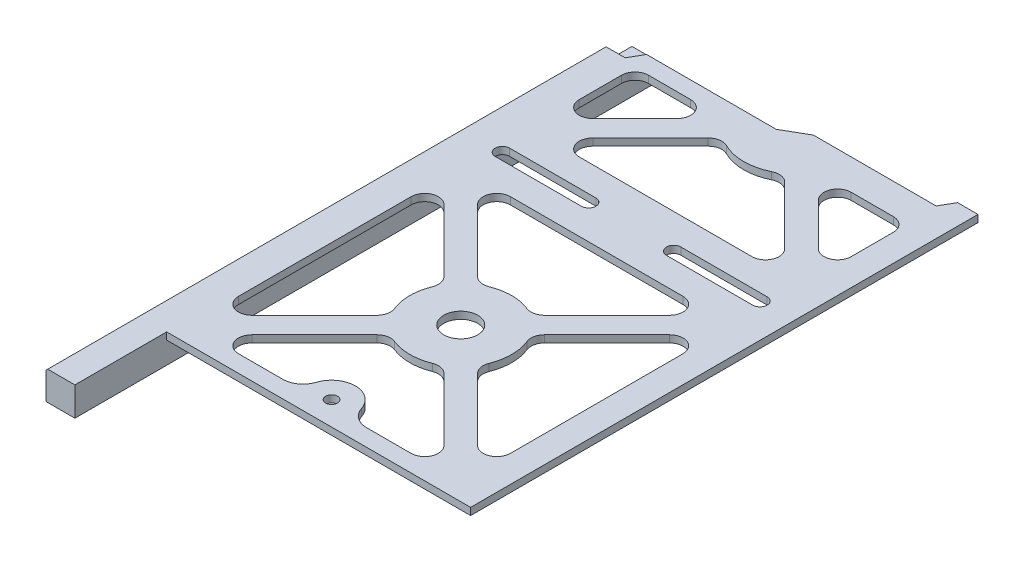
SolidWorks part; units mm, degrees
ref_plane "Front Plane" through (0, 0, 0) normal (0, 0, 1) x (1, 0, 0)
ref_plane "Top Plane" through (0, 0, 0) normal (0, 1, 0) x (1, 0, 0)
ref_plane "Right Plane" through (0, 0, 0) normal (1, 0, 0) x (0, 0, -1)
sketch "Sketch1" plane through (0, 0, 0) normal (0, 1, 0) x (1, 0, 0)
  line L0 (-48.95, -172.25) -> (-48.95, -8)
  line L2 (48.95, -7.35) -> (48.95, -165.25)
  line L5 (48.95, -165.25) -> (-40.45, -165.25)
  line L6 (-40.45, -165.25) -> (-40.45, -172.25)
  line L7 (-40.45, -172.25) -> (-48.95, -172.25)
  line L8 (-27.1718, -133.4216) -> (-8.8192, -115.0689)
  line L9 (-34.95, -9) -> (-22.5566, -9)
  line L10 (-38.95, -13) -> (-38.95, -25.3934)
  line L11 (-24.3434, -140.25) -> (26.4434, -140.25)
  line L12 (41.05, -13) -> (41.05, -25.3934)
  line L13 (-32.1216, -128.4718) -> (-13.7689, -110.1192)
  line L14 (29.2718, -133.4216) -> (10.9192, -115.0689)
  line L15 (34.2216, -128.4718) -> (15.8689, -110.1192)
  line L16 (15.8689, -90.3808) -> (34.2216, -72.0282)
  line L17 (-13.7689, -90.3808) -> (-32.1216, -72.0282)
  line L18 (10.9192, -85.4311) -> (29.2718, -67.0784)
  line L19 (-27.1718, -67.0784) -> (-8.8192, -85.4311)
  line L20 (-27.1718, -33.1716) -> (-10.2023, -16.2021)
  line L21 (-32.1216, -28.2218) -> (-19.7282, -15.8284)
  line L22 (29.2718, -33.1716) -> (12.3023, -16.2021)
  line L23 (34.2216, -28.2218) -> (21.8282, -15.8284)
  line L24 (41.05, -74.8566) -> (41.05, -125.6434)
  line L25 (-24.3434, -40) -> (26.4434, -40)
  line L29 (-38.95, -74.8566) -> (-38.95, -125.6434)
  line L34 (24.6566, -9) -> (37.05, -9)
  line L35 (41.05, -140.25) -> (-38.95, -60.25) construction
  line L36 (-38.95, -9) -> (41.05, -9) construction
  line L37 (-38.95, -9) -> (-38.95, -140.25) construction
  line L38 (-38.95, -140.25) -> (41.05, -140.25) construction
  line L39 (41.05, -9) -> (41.05, -140.25) construction
  line L40 (-38.95, -9) -> (41.05, -140.25) construction
  line L41 (-38.95, -140.25) -> (41.05, -9) construction
  line L42 (-38.95, -140.25) -> (41.05, -60.25) construction
  line L43 (1.05, 0) -> (-38.95, -40) construction
  line L44 (1.05, 0) -> (41.05, -40) construction
  line L45 (-24.3434, -60.25) -> (26.4434, -60.25)
  line L46 (-36.825, -50.125) -> (-11.45, -50.125) construction
  line L47 (-36.825, -48) -> (-11.45, -48)
  line L48 (-36.825, -52.25) -> (-11.45, -52.25)
  line L49 (13.55, -50.125) -> (38.925, -50.125) construction
  line L50 (13.55, -48) -> (38.925, -48)
  line L51 (13.55, -52.25) -> (38.925, -52.25)
  line L52 (-2.4141, -4) -> (4.5141, 0)
  line L53 (4.5141, 0) -> (-2.4141, 0) construction
  line L59 (-2.4141, -4) -> (-40.5406, -4)
  line L60 (-40.5406, -4) -> (-42.85, -8)
  line L61 (-42.85, -8) -> (-48.95, -8)
  line L62 (4.5141, 0) -> (40.6406, 0)
  line L63 (40.6406, 0) -> (42.95, 4)
  line L64 (42.95, 4) -> (48.95, 4)
  line L65 (48.95, 4) -> (48.95, -7.35)
  circle A0 centre (1.05, -100.25) radius 5
  arc A1 (-4.5085, -114.1821) -> (6.6085, -114.1821) centre (1.05, -100.25) ccw
  arc A2 (-5.6004, -15.4451) -> (7.7004, -15.4451) centre (1.05, -2) ccw
  arc A3 (-12.8821, -94.6915) -> (-12.8821, -105.8085) centre (1.05, -100.25) ccw
  arc A4 (6.6085, -86.3179) -> (-4.5085, -86.3179) centre (1.05, -100.25) ccw
  arc A5 (14.9821, -105.8085) -> (14.9821, -94.6915) centre (1.05, -100.25) ccw
  arc A8 (41.05, -125.6434) -> (34.2216, -128.4718) centre (37.05, -125.6434) cw
  arc A9 (26.4434, -140.25) -> (29.2718, -133.4216) centre (26.4434, -136.25) ccw
  arc A10 (41.05, -74.8566) -> (34.2216, -72.0282) centre (37.05, -74.8566) ccw
  arc A11 (26.4434, -60.25) -> (29.2718, -67.0784) centre (26.4434, -64.25) cw
  arc A12 (-24.3434, -60.25) -> (-27.1718, -67.0784) centre (-24.3434, -64.25) ccw
  arc A13 (-32.1216, -72.0282) -> (-38.95, -74.8566) centre (-34.95, -74.8566) ccw
  arc A14 (15.8689, -110.1192) -> (14.9821, -105.8085) centre (18.6973, -107.2907) cw
  arc A15 (15.8689, -90.3808) -> (14.9821, -94.6915) centre (18.6973, -93.2093) ccw
  arc A16 (10.9192, -85.4311) -> (6.6085, -86.3179) centre (8.0907, -82.6027) cw
  arc A17 (-4.5085, -86.3179) -> (-8.8192, -85.4311) centre (-5.9907, -82.6027) cw
  arc A18 (-12.8821, -94.6915) -> (-13.7689, -90.3808) centre (-16.5973, -93.2093) ccw
  arc A19 (-12.8821, -105.8085) -> (-13.7689, -110.1192) centre (-16.5973, -107.2907) cw
  arc A20 (10.9192, -115.0689) -> (6.6085, -114.1821) centre (8.0907, -117.8973) ccw
  arc A21 (-4.5085, -114.1821) -> (-8.8192, -115.0689) centre (-5.9907, -117.8973) ccw
  arc A22 (-32.1216, -128.4718) -> (-38.95, -125.6434) centre (-34.95, -125.6434) cw
  arc A23 (-24.3434, -140.25) -> (-27.1718, -133.4216) centre (-24.3434, -136.25) cw
  arc A24 (41.05, -13) -> (37.05, -9) centre (37.05, -13) ccw
  arc A25 (-34.95, -9) -> (-38.95, -13) centre (-34.95, -13) ccw
  arc A26 (-32.1216, -28.2218) -> (-38.95, -25.3934) centre (-34.95, -25.3934) cw
  arc A27 (-22.5566, -9) -> (-19.7282, -15.8284) centre (-22.5566, -13) cw
  arc A28 (24.6566, -9) -> (21.8282, -15.8284) centre (24.6566, -13) ccw
  arc A29 (41.05, -25.3934) -> (34.2216, -28.2218) centre (37.05, -25.3934) cw
  arc A30 (29.2718, -33.1716) -> (26.4434, -40) centre (26.4434, -36) cw
  arc A31 (-24.3434, -40) -> (-27.1718, -33.1716) centre (-24.3434, -36) cw
  arc A32 (12.3023, -16.2021) -> (7.7004, -15.4451) centre (9.4739, -19.0305) ccw
  arc A33 (-5.6004, -15.4451) -> (-10.2023, -16.2021) centre (-7.3739, -19.0305) ccw
  arc A34 (-36.825, -48) -> (-36.825, -52.25) centre (-36.825, -50.125) ccw
  arc A35 (-11.45, -52.25) -> (-11.45, -48) centre (-11.45, -50.125) ccw
  arc A36 (13.55, -48) -> (13.55, -52.25) centre (13.55, -50.125) ccw
  arc A37 (38.925, -52.25) -> (38.925, -48) centre (38.925, -50.125) ccw
  point P4 (-40.45, -168.75)
  point P28 (-24.1375, -50.125)
  point P45 (1.05, -74.625)
  point P49 (1.05, -100.25)
  point P60 (41.05, -65.1997)
  point P67 (-38.95, -65.1997)
  point P70 (13.8387, -108.089)
  point P75 (8.889, -87.4613)
  point P80 (-11.7387, -92.411)
  point P112 (26.2375, -50.125)
  dimension "D20" = 10
  dimension "D22" = 4
  dimension "D23" = 4
  dimension "D24" = 4
  dimension "D25" = 4
  dimension "D1" = 8.5
  dimension "D2" = 97.9
  dimension "D3" = 48.95
  dimension "D4" = 7
  dimension "D7" = 10
  dimension "D8" = 7.9
  dimension "D9" = 25
  dimension "D11" = 7
  dimension "D12" = 7
  dimension "D6" = 45
  dimension "D13" = 45
  dimension "D14" = 80
  dimension "D15" = 40
  dimension "D16" = 7
  dimension "D17" = 7
  dimension "D18" = 45
  dimension "D19" = 45
  dimension "D21" = 10
  dimension "D26" = 8
  dimension "D27" = 8
  dimension "D28" = 25
  dimension "D29" = 40
  dimension "D10" = 4
  dimension "D30" = 6.1
  dimension "D31" = 60
  dimension "D32" = 6
  dimension "D34" = 4
  dimension "D36" = 4
  dimension "D33" = 9
  dimension "D35" = 60
  dimension "D37" = 30
  dimension "D5" = 170.25
extrude "Boss-Extrude1" add sketch "Sketch1" along normal blind 2.1 contours L65 L64 L63 L62 L52 L59 L60 L61 L0 L7 L6 L5 L2 A37 L51 A36 L50 A35 L48 A34 L47 A33 A2 A32 L22 A30 L25 A31 L20 A15 L16 A10 L24 A8 L15 A14 A5 A0 A4 A17 L19 A12 L45 A11 L18 | L29 A22 L13 A19 A3 A18 L17 A13 | L21 A27 L9 A25 L10 A26 | A1 A20 L14 A9 L11 A23 L8 A21 | L23 A28 L34 A24 L12 A29
sketch "Sketch5" plane through (0, 0, 0) normal (0, -1, 0) x (1, 0, 0)
  line L0 (-48.95, 172.25) -> (-48.95, 8) construction
  line L1 (-40.45, 172.25) -> (-48.95, 172.25)
  line L2 (-40.45, 172.25) -> (-40.45, 2)
  line L3 (-40.45, 2) -> (-48.95, 2)
  line L4 (-48.95, 172.25) -> (-48.95, 2)
  line L5 (-40.45, 172.25) -> (-48.95, 2) construction
  line L6 (-40.45, 2) -> (-48.95, 172.25) construction
  line L7 (1.05, 2) -> (-48.95, 2) construction
  line L8 (-2.4141, 4) -> (4.5141, 0) construction
  point P4 (-44.7, 87.125)
extrude "Boss-Extrude3" add sketch "Sketch5" along normal blind 6.4
sketch "Sketch6" plane through (-48.95, 0, 0) normal (-1, 0, 0) x (0, 0, 1)
  line L0 (172.25, -6.4) -> (2, -6.4) construction
  line L1 (2, 0) -> (145.35, 0)
  line L2 (2, 0) -> (2, -6.4)
  line L3 (2, -6.4) -> (145.35, -6.4)
  line L4 (145.35, 0) -> (145.35, -6.4)
  line L5 (2, 0) -> (145.35, -6.4) construction
  line L6 (2, -6.4) -> (145.35, 0) construction
  line L8 (140.25, 2.1) -> (140.25, 0) construction
  line L9 (140.25, 2.1) -> (140.25, 0)
  point P4 (73.675, -3.2)
  line M7 (8, 0) -> (2, 0)
  line M8 (2, 0) -> (2, -6.4)
  line M9 (2, -6.4) -> (172.25, -6.4)
  dimension "D1" = 5.1
extrude "Cut-Extrude2" cut sketch "Sketch6" against normal blind 2.1 contours L4 L1 M7 M8 M9
sketch "Sketch7" plane through (0, 0, 0) normal (0, -1, 0) x (1, 0, 0)
  line L0 (1.05, 2) -> (48.95, 2) construction
  line L1 (-2.4141, 4) -> (4.5141, 0) construction
  line L2 (48.95, -4) -> (48.95, 165.25) construction
  line L4 (16.05, 3.25) -> (26.05, 3.25)
  line L5 (16.05, 3.25) -> (16.05, 0.75)
  line L6 (16.05, 0.75) -> (26.05, 0.75)
  line L7 (26.05, 3.25) -> (26.05, 0.75)
  line L8 (16.05, 3.25) -> (26.05, 0.75) construction
  line L9 (16.05, 0.75) -> (26.05, 3.25) construction
  point P10 (21.05, 2)
  dimension "D1" = 2.5
  dimension "D2" = 10
  dimension "D3" = 15
extrude "Boss-Extrude4" add sketch "Sketch7" along normal blind 3
chamfer "Chamfer1" distance 0.5 angle 45 1 edges at (-48.95, 2.1, 90.125)
sketch "Sketch8" plane through (0, 2.1, 0) normal (0, 1, 0) x (1, 0, 0)
  line L1 (-40.45, -165.25) -> (48.95, -165.25)
  line L2 (-40.45, -165.25) -> (-40.45, -145.25)
  line L3 (-40.45, -145.25) -> (48.95, -145.25)
  line L4 (48.95, -165.25) -> (48.95, -145.25)
  line L5 (-40.45, -165.25) -> (48.95, -145.25) construction
  line L6 (-40.45, -145.25) -> (48.95, -165.25) construction
  line L8 (48.95, 4) -> (48.95, -165.25) construction
  point P4 (4.25, -155.25)
  dimension "D2" = 20
extrude "Cut-Extrude3" cut sketch "Sketch8" against normal through all
sketch "Sketch9" plane through (0, 2.1, 0) normal (0, 1, 0) x (1, 0, 0)
  line L3 (-16.537, -140.25) -> (-11.3193, -140.25)
  line L4 (-24.3434, -140.25) -> (26.4434, -140.25) construction
  line L6 (1.05, -100.25) -> (1.05, -150.0937) construction
  line L7 (13.4193, -140.25) -> (15.2362, -140.25)
  line L8 (-11.3193, -140.25) -> (13.4193, -140.25)
  circle A5 centre (1.05, -138.25) radius 1.75
  arc A6 (7.7104, -136.0962) -> (-5.6104, -136.0962) centre (1.05, -138.25) ccw
  arc A7 (13.4193, -140.25) -> (7.7104, -136.0962) centre (13.4193, -134.25) cw
  arc A8 (-5.6104, -136.0962) -> (-11.3193, -140.25) centre (-11.3193, -134.25) cw
  dimension "D1" = 6
  dimension "D2" = 2
  dimension "D3" = 3.5
  dimension "D4" = 7
extrude "Boss-Extrude8" add sketch "Sketch9" against normal up to surface (2.1 mm away) contours L6 A6 A8 L8 A5 | A6 L6 A5 L8 A7 up to face at (12.8363, 0, 36.3125)
equation "\"D12@Sketch1\"=\"D11@Sketch1\""
equation "\"D16@Sketch1\"=\"D11@Sketch1\""
equation "\"D17@Sketch1\"=\"D11@Sketch1\""
equation "\"D19@Sketch1\"=\"D18@Sketch1\""
equation "\"D13@Sketch1\"=\"D6@Sketch1\""
equation "\"D15@Sketch1\"=\"D14@Sketch1\"/2"
equation "\"D22@Sketch1\"=\"D23@Sketch1\""
equation "\"D29@Sketch1\"=\"D15@Sketch1\""
equation "\"D36@Sketch1\"=\"D34@Sketch1\""
equation "\"D1@Boss-Extrude3\"=8.5-2.1"
